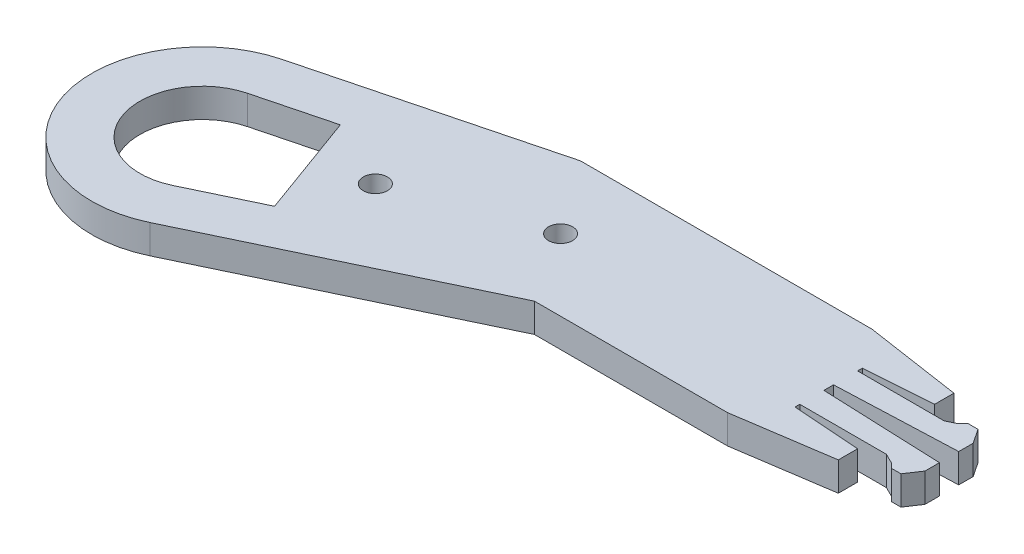
SolidWorks part; units mm, degrees
material "Lasercut ABS"
ref_plane "Front Plane" through (0, 0, 0) normal (0, 0, 1) x (1, 0, 0)
ref_plane "Top Plane" through (0, 0, 0) normal (0, 1, 0) x (1, 0, 0)
ref_plane "Right Plane" through (0, 0, 0) normal (1, 0, 0) x (0, 0, -1)
sketch "Sketch4" plane through (0, 0, 0) normal (0, 1, 0) x (1, 0, 0)
  line L0 (0, 0) -> (0, 17.2192) construction
  line L1 (-2.8794, 11.1337) -> (21.7373, 17.5)
  line L2 (4.9509, -10.3797) -> (31.9538, 2.5)
  line L3 (52, 2.5) -> (31.9538, 2.5)
  line L4 (52, 17.5) -> (21.7373, 17.5)
  arc A0 (-2.8794, 11.1337) -> (4.9509, -10.3797) centre (0, 0) ccw
  line B0 (6.0339, 8.2743) -> (9.9409, -2.46)
  line B1 (0, 0) -> (7.9874, 2.9072) construction
  line B2 (6.0339, 8.2743) -> (-1.6275, 6.293)
  line B3 (9.9409, -2.46) -> (2.7983, -5.8668)
  arc B4 (-1.6275, 6.293) -> (2.7983, -5.8668) centre (0, 0) ccw
  circle B5 centre (13.1557, 4.7883) radius 1.25
  circle B6 centre (27.2511, 9.9186) radius 1.25
  line B7 (52, 10) -> (55, 10) construction
  line B8 (55, 10.5) -> (55, 9.5)
  line B9 (55, 10.5) -> (67.5, 11)
  line B10 (67.5, 11) -> (67.5, 12.5)
  line B11 (67.5, 12.5) -> (66.5, 14)
  line B12 (66.5, 14) -> (65.5, 14)
  line B13 (65.5, 14) -> (65, 13.5)
  line B14 (65, 13.5) -> (64, 13)
  line B15 (64, 13) -> (55, 13)
  line B16 (55, 13) -> (55, 13.5)
  line B17 (55, 13.5) -> (62, 14)
  line B18 (62, 14) -> (62, 16)
  line B19 (62, 16) -> (52, 17.5)
  line B20 (55, 9.5) -> (67.5, 9)
  line B21 (67.5, 9) -> (67.5, 7.5)
  line B22 (67.5, 7.5) -> (66.5, 6)
  line B23 (66.5, 6) -> (65.5, 6)
  line B24 (65.5, 6) -> (65, 6.5)
  line B25 (65, 6.5) -> (64, 7)
  line B26 (64, 7) -> (55, 7)
  line B27 (55, 7) -> (55, 6.5)
  line B28 (55, 6.5) -> (62, 6)
  line B29 (62, 6) -> (62, 4)
  line B30 (62, 4) -> (52, 2.5)
  dimension "D1" = 70
  dimension "D2" = 5
  dimension "D3" = 10
  dimension "D4" = 62
sketch_block_instance "Block-Horn-TowerPro-1"
sketch_block "Block1" parameters "D1"=6.5, "D4"=2.5, "D2"=15, "D3"=11, "D5"=14, "D6"=15
sketch_block_instance "Block-Snap-Textile-1"
sketch_block "Block-Snap-Textile" parameters "D1"=3, "D2"=1, "D3"=2, "D4"=1.5, "D5"=10, "D6"=0.5, "D7"=9, "D8"=1, "D9"=0.5, "D10"=0.5, "D11"=0.5, "D12"=1, "D13"=12.5, "D14"=0.5, "D15"=0.5, "D16"=1.5, "D17"=1.5
extrude "Boss-Extrude2" add sketch "Sketch4" against normal blind 3 contours L0 A0 L2 L3 B30 B29 B28 B27 B26 B25 B24 B23 B22 B21 B20 B8 B9 B10 B11 B12 B13 B14 B15 B16 B17 B18 B19 L4 L1 B2 B0 B3 B4 B6 B5 | A0 L0 B4 B2 L1
sketch "Sketch5" plane through (0, 0, 0) normal (0, 1, 0) x (1, 0, 0)
  line L0 (4.8313, 11.5785) -> (20.3217, 15.5845) construction
  line L1 (10.4563, -3.876) -> (24.8976, 3.0121) construction
  line L2 (6.0339, 8.2743) -> (9.9409, -2.46) construction
  line L3 (-2.8794, 11.1337) -> (21.7373, 17.5) construction
  line L4 (4.9509, -10.3797) -> (31.9538, 2.5) construction
  text T0 "ONO V2" font "1CamBam_Stick_3" height 2.5
  text T1 "EB6" font "1CamBam_Stick_3" height 2.5
  dimension "D1" = 16
  dimension "D2" = 1.5
  dimension "D3" = 3.5
equation "\"X\"= 10"
equation "\"Y\"= 62"
equation "\"D3@Sketch4\"=\"X\""
equation "\"D4@Sketch4\"=\"Y\""
